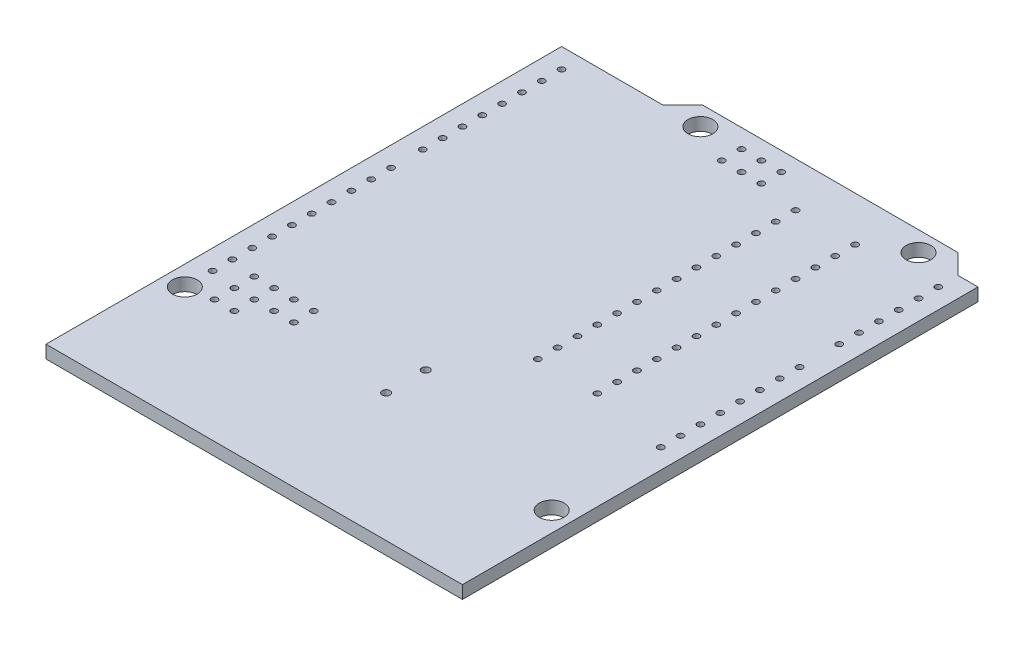
SolidWorks part; units mm, degrees
ref_plane "Front Plane" through (0, 0, 0) normal (0, 0, 1) x (1, 0, 0)
ref_plane "Top Plane" through (0, 0, 0) normal (0, 1, 0) x (1, 0, 0)
ref_plane "Right Plane" through (0, 0, 0) normal (1, 0, 0) x (0, 0, -1)
ref_plane "Plane1" through (0, -1.65, 0) normal (0, -1, 0) x (1, 0, 0)
sketch "Sketch1" plane through (0, -1.65, 0) normal (0, -1, 0) x (1, 0, 0)
  line L0 (-5.08, -68.58) -> (-2.54, -66.04)
  line L1 (-2.54, -66.04) -> (0, -66.04)
  line L2 (0, -66.04) -> (0, 0)
  line L3 (0, 0) -> (-53.34, 0)
  line L4 (-53.34, 0) -> (-53.34, -66.04)
  line L5 (-53.34, -66.04) -> (-40.386, -66.04)
  line L6 (-40.386, -66.04) -> (-37.846, -68.58)
  line L7 (-37.846, -68.58) -> (-5.08, -68.58)
  circle A0 centre (-50.8, -63.5) radius 0.4
  circle A1 centre (-50.8, -60.96) radius 0.4
  circle A2 centre (-50.8, -58.42) radius 0.4
  circle A3 centre (-50.8, -55.88) radius 0.4
  circle A4 centre (-50.8, -53.34) radius 0.4
  circle A5 centre (-50.8, -50.8) radius 0.4
  circle A6 centre (-50.8, -41.656) radius 0.4
  circle A7 centre (-50.8, -39.116) radius 0.4
  circle A8 centre (-50.8, -36.576) radius 0.4
  circle A9 centre (-50.8, -34.036) radius 0.4
  circle A10 centre (-50.8, -31.496) radius 0.4
  circle A11 centre (-50.8, -28.956) radius 0.4
  circle A12 centre (-50.8, -26.416) radius 0.4
  circle A13 centre (-50.8, -23.876) radius 0.4
  circle A14 centre (-2.54, -63.5) radius 0.4
  circle A15 centre (-2.54, -60.96) radius 0.4
  circle A16 centre (-2.54, -58.42) radius 0.4
  circle A17 centre (-2.54, -55.88) radius 0.4
  circle A18 centre (-2.54, -53.34) radius 0.4
  circle A19 centre (-2.54, -50.8) radius 0.4
  circle A20 centre (-2.54, -45.72) radius 0.4
  circle A21 centre (-2.54, -43.18) radius 0.4
  circle A22 centre (-2.54, -40.64) radius 0.4
  circle A23 centre (-2.54, -38.1) radius 0.4
  circle A24 centre (-2.54, -35.56) radius 0.4
  circle A25 centre (-2.54, -33.02) radius 0.4
  circle A26 centre (-7.62, -66.04) radius 1.5875
  circle A27 centre (-35.56, -66.04) radius 1.5875
  circle A28 centre (-2.54, -13.97) radius 1.5875
  circle A29 centre (-50.8, -15.24) radius 1.5875
  circle A30 centre (-2.54, -27.94) radius 0.4
  circle A31 centre (-50.8, -18.796) radius 0.4
  circle A32 centre (-2.54, -30.48) radius 0.4
  circle A33 centre (-50.8, -45.72) radius 0.4
  circle A34 centre (-50.8, -21.336) radius 0.4
  circle A35 centre (-50.8, -48.26) radius 0.4
  circle A36 centre (-30.43, -66.18) radius 0.4
  circle A37 centre (-27.89, -66.18) radius 0.4
  circle A38 centre (-25.35, -66.18) radius 0.4
  circle A39 centre (-25.35, -63.64) radius 0.4
  circle A40 centre (-27.89, -63.64) radius 0.4
  circle A41 centre (-30.43, -63.64) radius 0.4
  circle A42 centre (-47.498, -15.748) radius 0.4
  circle A43 centre (-47.498, -18.288) radius 0.4
  circle A44 centre (-47.498, -20.828) radius 0.4
  circle A45 centre (-44.958, -20.828) radius 0.4
  circle A46 centre (-44.958, -18.288) radius 0.4
  circle A47 centre (-44.958, -15.748) radius 0.4
  circle A48 centre (-42.418, -18.288) radius 0.4
  circle A49 centre (-42.418, -20.828) radius 0.4
  circle A50 centre (-39.878, -20.828) radius 0.4
  circle A51 centre (-39.878, -18.288) radius 0.4
  circle A52 centre (-26.162, -21.463) radius 0.5
  circle A53 centre (-26.162, -16.383) radius 0.5
  circle A54 centre (-20.193, -29.845) radius 0.4
  circle A55 centre (-12.573, -29.845) radius 0.4
  circle A56 centre (-20.193, -32.385) radius 0.4
  circle A57 centre (-12.573, -32.385) radius 0.4
  circle A58 centre (-20.193, -34.925) radius 0.4
  circle A59 centre (-12.573, -34.925) radius 0.4
  circle A60 centre (-20.193, -37.465) radius 0.4
  circle A61 centre (-12.573, -37.465) radius 0.4
  circle A62 centre (-20.193, -40.005) radius 0.4
  circle A63 centre (-12.573, -40.005) radius 0.4
  circle A64 centre (-20.193, -42.545) radius 0.4
  circle A65 centre (-12.573, -42.545) radius 0.4
  circle A66 centre (-20.193, -45.085) radius 0.4
  circle A67 centre (-12.573, -45.085) radius 0.4
  circle A68 centre (-20.193, -47.625) radius 0.4
  circle A69 centre (-12.573, -47.625) radius 0.4
  circle A70 centre (-20.193, -50.165) radius 0.4
  circle A71 centre (-12.573, -50.165) radius 0.4
  circle A72 centre (-20.193, -52.705) radius 0.4
  circle A73 centre (-12.573, -52.705) radius 0.4
  circle A74 centre (-20.193, -55.245) radius 0.4
  circle A75 centre (-12.573, -55.245) radius 0.4
  circle A76 centre (-20.193, -57.785) radius 0.4
  circle A77 centre (-12.573, -57.785) radius 0.4
  circle A78 centre (-20.193, -60.325) radius 0.4
  circle A79 centre (-12.573, -60.325) radius 0.4
  circle A80 centre (-20.193, -62.865) radius 0.4
  circle A81 centre (-12.573, -62.865) radius 0.4
extrude "Boss-Extrude1" add sketch "Sketch1" against normal blind 1.65
